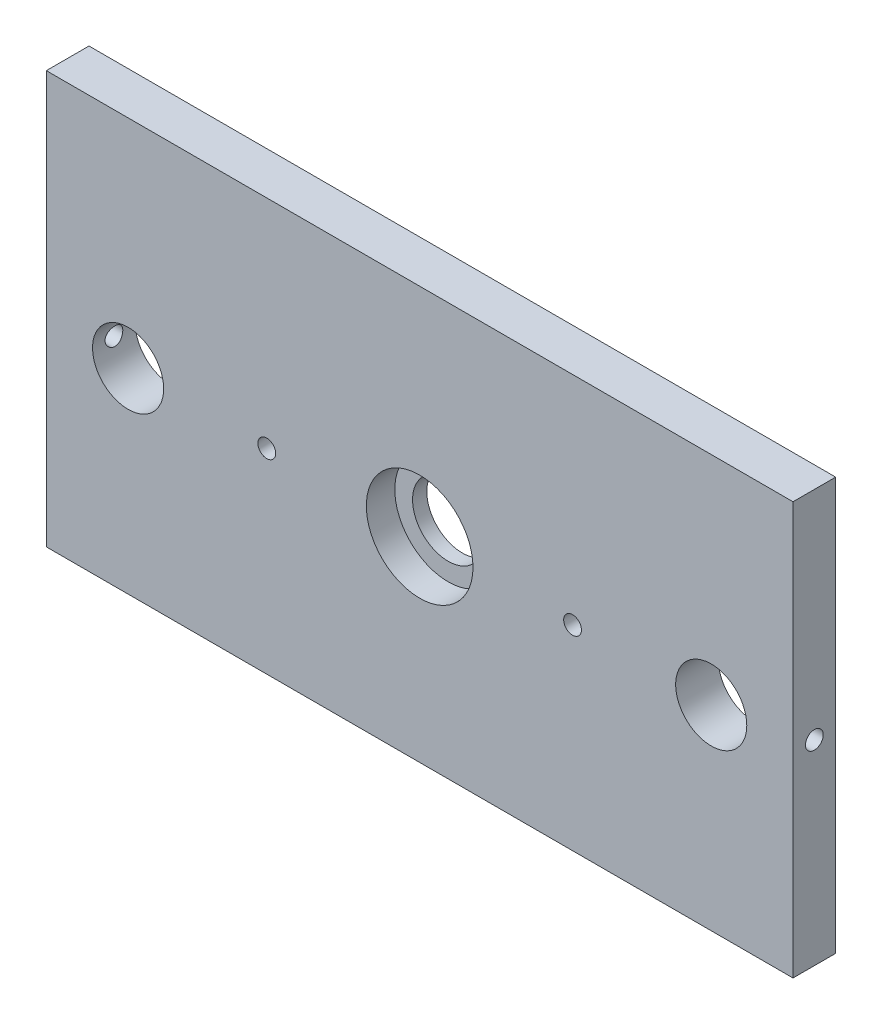
SolidWorks part; units mm, degrees
ref_plane "Front Plane" through (0, 0, 0) normal (0, 0, 1) x (1, 0, 0)
ref_plane "Top Plane" through (0, 0, 0) normal (0, 1, 0) x (1, 0, 0)
ref_plane "Right Plane" through (0, 0, 0) normal (1, 0, 0) x (0, 0, -1)
sketch "Sketch1" plane through (0, 0, 0) normal (0, 1, 0) x (1, 0, 0)
  line L1 (0, 0) -> (210, 0)
  line L2 (0, 0) -> (0, 12)
  line L3 (0, 12) -> (210, 12)
  line L4 (210, 0) -> (210, 12)
  dimension "D1" = 12
  dimension "D2" = 210
extrude "Boss-Extrude1" add sketch "Sketch1" along normal blind 116
sketch "Sketch2" plane through (0, 0, 0) normal (0, 0, 1) x (1, 0, 0)
  line L0 (0, 0) -> (210, 0) construction
  line L1 (0, 116) -> (0, 0) construction
  line L2 (210, 116) -> (210, 0) construction
  circle A0 centre (23, 55) radius 10
  circle A1 centre (187, 55) radius 10
  dimension "D1" = 55
  dimension "D2" = 55
  dimension "D3" = 23
  dimension "D4" = 23
extrude "Cut-Extrude1" cut sketch "Sketch2" against normal through all
hole_wizard "Ø5.0mm Dowel Hole1" positions "Sketch4" profile "Sketch3" hole size "Ø5.0" standard "ANSI Metric"
sketch "Sketch4" plane through (0, 0, 0) normal (-1, 0, 0) x (0, 0, 1)
  line L0 (-12, 116) -> (-12, 0) construction
  line L1 (-12, 0) -> (0, 0) construction
  point P0 (-6, 55)
  dimension "D1" = 6
  dimension "D2" = 55
sketch "Sketch3" plane through (0, 55, -6) normal (0, 1, 0) x (0, 0, 1)
  line L0 (0, 0) -> (0, 26.5022)
  line L1 (0, 26.5022) -> (2.5, 25)
  line L2 (2.5, 25) -> (2.5, 0)
  line L5 (2.5, 0) -> (0, 0)
  line L10 (0, 26.5022) -> (-2.5, 25) construction
  line L11 (0, -6.35) -> (0, 107.95) construction
  dimension "Hole Dia." = 5
  dimension "Hole Depth" = 25
  dimension "Drill Angle" = 118
hole_wizard "Ø5.0mm Dowel Hole2" positions "Sketch6" profile "Sketch5" hole size "Ø5.0" standard "ANSI Metric"
sketch "Sketch6" plane through (210, 0, 0) normal (1, 0, 0) x (0, 0, -1)
  line L0 (0, 0) -> (12, 0) construction
  line L1 (0, 116) -> (0, 0) construction
  point P0 (6, 55)
  point P11 (6.7946, 117.3717)
  dimension "D1" = 55
  dimension "D2" = 6
sketch "Sketch5" plane through (210, 55, -6) normal (0, 1, 0) x (0, 0, -1)
  line L0 (0, 0) -> (0, 26.5022)
  line L1 (0, 26.5022) -> (2.5, 25)
  line L2 (2.5, 25) -> (2.5, 0)
  line L5 (2.5, 0) -> (0, 0)
  line L10 (0, 26.5022) -> (-2.5, 25) construction
  line L11 (0, -6.35) -> (0, 107.95) construction
  dimension "Hole Dia." = 5
  dimension "Hole Depth" = 25
  dimension "Drill Angle" = 118
sketch "Sketch7" plane through (0, 0, 0) normal (0, 0, 1) x (1, 0, 0)
  line L0 (0, 0) -> (210, 0) construction
  line L1 (0, 116) -> (0, 0) construction
  circle A0 centre (105, 55) radius 10
  dimension "D1" = 20
  dimension "D2" = 55
  dimension "D3" = 105
extrude "Cut-Extrude2" cut sketch "Sketch7" against normal through all
sketch "Sketch8" plane through (0, 0, 0) normal (0, 0, 1) x (1, 0, 0)
  circle A0 centre (105, 55) radius 15
  dimension "D1" = 30
extrude "Cut-Extrude3" cut sketch "Sketch8" against normal blind 8
hole_wizard "Ø5.0mm Dowel Hole3" positions "Sketch10" profile "Sketch9" hole size "Ø5.0" standard "ANSI Metric"
sketch "Sketch10" plane through (0, 0, 0) normal (0, -1, 0) x (-1, 0, 0)
  line L0 (-210, 12) -> (0, 12) construction
  line L1 (-210, 0) -> (-210, 12) construction
  line L2 (0, 12) -> (0, 0) construction
  point P0 (-25, 6)
  point P2 (-105, 6)
  point P4 (-185, 6)
  dimension "D1" = 6
  dimension "D2" = 6
  dimension "D3" = 6
  dimension "D4" = 25
  dimension "D5" = 25
  dimension "D6" = 105
sketch "Sketch9" plane through (25, 0, -6) normal (1, 0, 0) x (0, 0, -1)
  line L0 (0, 0) -> (0, 13.5022)
  line L1 (0, 13.5022) -> (2.5, 12)
  line L2 (2.5, 12) -> (2.5, 0)
  line L5 (2.5, 0) -> (0, 0)
  line L10 (0, 13.5022) -> (-2.5, 12) construction
  line L11 (0, -6.35) -> (0, 107.95) construction
  dimension "Hole Dia." = 5
  dimension "Hole Depth" = 12
  dimension "Drill Angle" = 118
hole_wizard "Ø5.0mm Dowel Hole4" positions "Sketch12" profile "Sketch11" hole size "Ø5.0" standard "ANSI Metric"
sketch "Sketch12" plane through (0, 0, -12) normal (0, 0, -1) x (-1, 0, 0)
  line L0 (-210, 0) -> (0, 0) construction
  circle A0 centre (-105, 55) radius 10 construction
  point P0 (-148, 55)
  point P2 (-62, 55)
  dimension "D1" = 55
  dimension "D2" = 55
  dimension "D3" = 86
  dimension "D4" = 43
sketch "Sketch11" plane through (148, 55, -12) normal (1, 0, 0) x (0, 1, 0)
  line L0 (0, 0) -> (0, 26.5022)
  line L1 (0, 26.5022) -> (2.5, 25)
  line L2 (2.5, 25) -> (2.5, 0)
  line L5 (2.5, 0) -> (0, 0)
  line L10 (0, 26.5022) -> (-2.5, 25) construction
  line L11 (0, -6.35) -> (0, 107.95) construction
  dimension "Hole Dia." = 5
  dimension "Hole Depth" = 25
  dimension "Drill Angle" = 118
